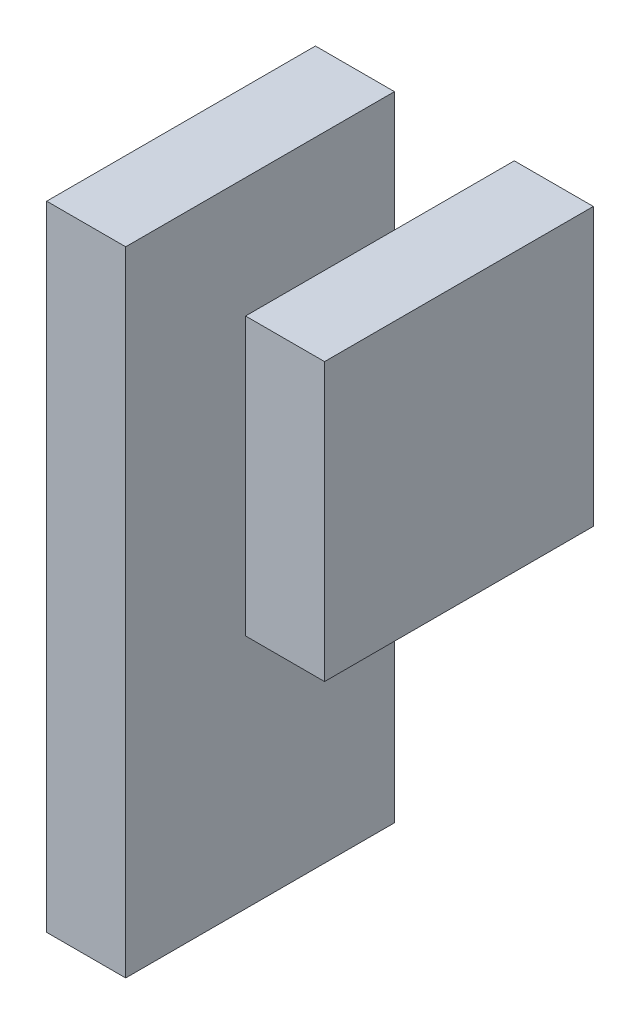
SolidWorks part; units mm, degrees
ref_plane "Ebene vorne" through (0, 0, 0) normal (0, 0, 1) x (1, 0, 0)
ref_plane "Ebene oben" through (0, 0, 0) normal (0, 1, 0) x (1, 0, 0)
ref_plane "Ebene rechts" through (0, 0, 0) normal (1, 0, 0) x (0, 0, -1)
sketch "Skizze2" plane through (0, 0, 0) normal (0, 0, 1) x (1, 0, 0)
  line L0 (157.7175, -54.4425) -> (155.6875, -54.4425) construction
  line L1 (147.8325, -54.4425) -> (150.7725, -54.4425)
  line L2 (147.8325, -54.4425) -> (147.8325, -78.005)
  line L3 (147.8325, -78.005) -> (150.7725, -78.005)
  line L4 (150.7725, -54.4425) -> (150.7725, -78.005)
  line L5 (158.1725, -64.7525) -> (155.2325, -64.7525)
  line L6 (158.1725, -64.7525) -> (158.1725, -54.4425)
  line L7 (158.1725, -54.4425) -> (155.2325, -54.4425)
  line L8 (155.2325, -64.7525) -> (155.2325, -54.4425)
  line L9 (155.6875, -64.7525) -> (157.7175, -64.7525) construction
  line L10 (148.285, -78.005) -> (150.315, -78.005) construction
  arc A0 (157.7175, -60.0525) -> (157.7175, -59.1425) centre (157.7175, -59.5975) ccw construction
  arc A1 (155.6875, -54.4425) -> (155.6875, -55.3525) centre (155.6875, -54.8975) ccw construction
  arc A2 (150.3175, -55.355) -> (150.3175, -54.445) centre (150.3175, -54.9) ccw construction
  arc A3 (148.2875, -59.145) -> (148.2875, -60.055) centre (148.2875, -59.6) ccw construction
extrude "Aufsatz-Linear austragen1" add sketch "Skizze2" along normal blind 10
